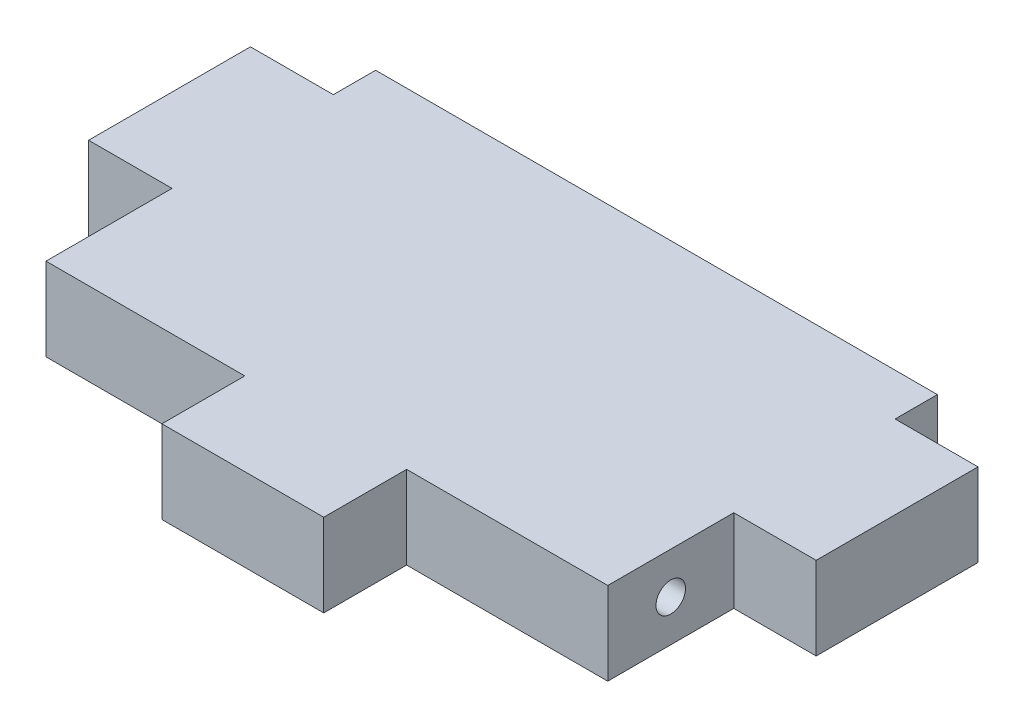
SolidWorks part; units mm, degrees
ref_plane "Front Plane" through (0, 0, 0) normal (0, 0, 1) x (1, 0, 0)
ref_plane "Top Plane" through (0, 0, 0) normal (0, 1, 0) x (1, 0, 0)
ref_plane "Right Plane" through (0, 0, 0) normal (1, 0, 0) x (0, 0, -1)
sketch "Sketch2" plane through (0, 0, 0) normal (0, 1, 0) x (1, 0, 0)
  line L0 (0, 0) -> (0, -38.3664) construction
  line L1 (-21.4249, -15.9122) -> (-6.1976, -15.9122)
  line L2 (-21.4249, -15.9122) -> (-21.4249, -6.2602)
  line L3 (6.1976, -15.9122) -> (21.6027, -15.9122)
  line L4 (21.5642, 9.3735) -> (21.5642, 6.135)
  line L6 (6.1976, -15.9122) -> (6.1976, -22.2622)
  line L8 (21.6027, -6.2602) -> (21.6027, -15.9122)
  line L9 (21.5642, 6.135) -> (27.9142, 6.135)
  line L10 (21.5642, 12.4215) -> (8.8642, 12.4215) construction
  line L11 (21.6027, -6.2602) -> (27.9142, -6.2602)
  line L12 (27.9142, 6.135) -> (27.9142, -6.2602)
  line L13 (8.8642, 12.4215) -> (8.8642, 9.3735) construction
  line L14 (21.5642, 9.3735) -> (-21.4634, 9.3735)
  line L16 (8.9265, -12.5826) -> (8.9207, -9.5346) construction
  line L17 (21.6264, -12.5586) -> (8.9265, -12.5826) construction
  line L18 (8.9207, -9.5346) -> (21.6207, -9.5106) construction
  line L19 (-21.4249, -6.2602) -> (-27.8134, -6.2602)
  line L20 (-27.8134, 6.135) -> (-27.8134, -6.2602)
  line L21 (-21.4634, 6.135) -> (-27.8134, 6.135)
  line L22 (-21.4634, 9.3735) -> (-21.4634, 6.135)
  line L23 (6.1976, -22.2622) -> (-6.1976, -22.2622)
  line L24 (-6.1976, -22.2622) -> (-6.1976, -15.9122)
  line L25 (-27.8134, -0.0262) -> (45.8466, 0) construction
  line L26 (12.9495, -9.527) -> (21.6027, -15.9122) construction
  dimension "D1" = 12.3952
  dimension "D2" = 6.35
  dimension "D3" = 3.048
  dimension "D4" = 6.35
  dimension "D5" = 12.3952
  dimension "D6" = 43.0276
  dimension "D7" = 15.2273
  dimension "D8" = 12.3952
  dimension "D9" = 6.1976
extrude "Boss-Extrude1" add sketch "Sketch2" along normal blind 6.35
sketch "Sketch3" plane through (21.6027, 0, 0) normal (1, 0, 0) x (0, 0, -1)
  line L0 (-6.2602, 3.175) -> (-15.9122, 3.175) construction
  line L1 (-6.2602, 6.35) -> (-6.2602, 0) construction
  line L2 (-15.9122, 6.35) -> (-15.9122, 0) construction
  line L3 (-11.0862, 6.35) -> (-11.0862, 0) construction
  line L4 (-15.9122, 6.35) -> (-6.2602, 6.35) construction
  line L5 (-15.9122, 0) -> (-6.2602, 0) construction
  circle A0 centre (-11.0862, 3.175) radius 1.1303
  dimension "D1" = 2.2606
extrude "Cut-Extrude1" cut sketch "Sketch3" against normal blind 12.7
mirror "Mirror1" about plane through (0, 0, 0) normal (1, 0, 0) of "Cut-Extrude1"
